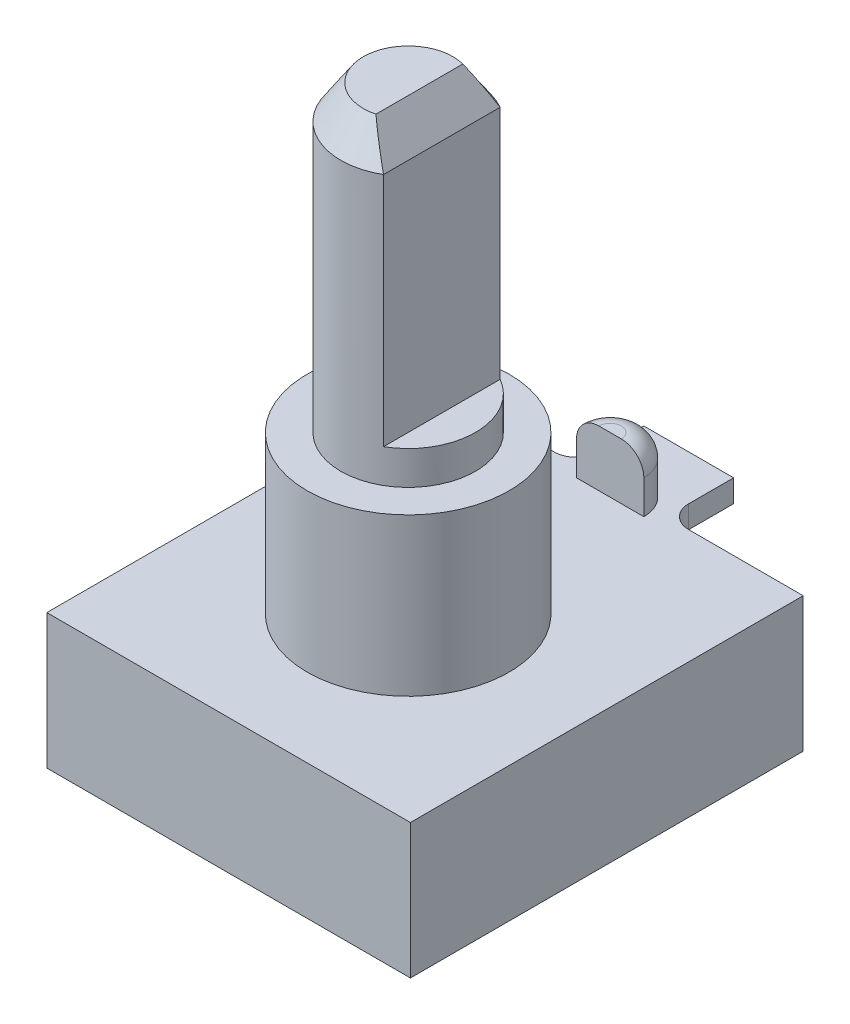
SolidWorks part; units mm, degrees
ref_plane "Front Plane" through (0, 0, 0) normal (0, 0, 1) x (1, 0, 0)
ref_plane "Top Plane" through (0, 0, 0) normal (0, 1, 0) x (1, 0, 0)
ref_plane "Right Plane" through (0, 0, 0) normal (1, 0, 0) x (0, 0, -1)
sketch "Sketch1" plane through (0, 0, 0) normal (0, 1, 0) x (1, 0, 0)
  line L1 (-8.1, 8.75) -> (8.1, 8.75)
  line L2 (-8.1, 8.75) -> (-8.1, -8.75)
  line L3 (-8.1, -8.75) -> (8.1, -8.75)
  line L4 (8.1, 8.75) -> (8.1, -8.75)
  line L5 (-8.1, 8.75) -> (8.1, -8.75) construction
  line L6 (-8.1, -8.75) -> (8.1, 8.75) construction
  point P0 (0, 0)
  dimension "D1" = 17.5
  dimension "D2" = 16.2
extrude "Boss-Extrude1" add sketch "Sketch1" along normal blind 6
sketch "Sketch2" plane through (0, 0, 0) normal (0, -1, 0) x (1, 0, 0)
  line L1 (-6, -6) -> (6, -6)
  line L2 (-6, -6) -> (-6, 6)
  line L3 (-6, 6) -> (6, 6)
  line L4 (6, -6) -> (6, 6)
  line L5 (-6, -6) -> (6, 6) construction
  line L6 (-6, 6) -> (6, -6) construction
  point P0 (0, 0)
  dimension "D1" = 12
  dimension "D2" = 12
extrude "Boss-Extrude2" add sketch "Sketch2" along normal blind 1.5
sketch "Sketch3" plane through (0, 6, 0) normal (0, 1, 0) x (1, 0, 0)
  line L0 (8.1, 8.75) -> (-8.1, 8.75) construction
  circle A0 centre (0, -0.75) radius 4.5
  dimension "D1" = 9
  dimension "D2" = 9.5
extrude "Boss-Extrude3" add sketch "Sketch3" along normal blind 7
sketch "Sketch4" plane through (0, 13, 0) normal (0, 1, 0) x (1, 0, 0)
  circle A0 centre (0, -0.75) radius 3
  dimension "D1" = 6
extrude "Boss-Extrude4" add sketch "Sketch4" along normal blind 13.5
sketch "Sketch5" plane through (0, 26.5, 0) normal (0, 1, 0) x (1, 0, 0)
  line L0 (1.5, 1.8481) -> (1.5, -3.3481)
  circle A0 centre (0, -0.75) radius 3 construction
  arc A1 (1.5, 1.8481) -> (1.5, -3.3481) centre (0, -0.75) ccw
  arc A2 (1.5, 1.8481) -> (1.5, -3.3481) centre (0, -0.75) cw
  point P6 (-3, -0.75)
  circle M3 centre (0, -0.75) radius 3
  dimension "D1" = 4.5
  dimension "D2" = 3
extrude "Cut-Extrude1" cut sketch "Sketch5" against normal blind 12 contours L0 M3
sketch "Sketch6" plane through (0, 0, -8.75) normal (0, 0, -1) x (-1, 0, 0)
  line L0 (-8.1, 6) -> (8.1, 6) construction
  line L1 (-2, 5) -> (2, 5)
  line L2 (-2, 5) -> (-2, 6)
  line L3 (-2, 6) -> (2, 6)
  line L4 (2, 5) -> (2, 6)
  line L5 (-2, 5) -> (2, 6) construction
  line L6 (-2, 6) -> (2, 5) construction
  line L7 (-8.1, 0) -> (8.1, 0) construction
  point P0 (0, 5.5)
  point P9 (0, 0)
  dimension "D1" = 1
  dimension "D2" = 4
  dimension "D3" = 0
extrude "Boss-Extrude5" add sketch "Sketch6" along normal blind 3
fillet "Fillet1" radius 1 2 edges at (-2, 5.5, -8.75) (2, 5.5, -8.75)
chamfer "Chamfer1" distance 1.5 distance2 1 1 edges at (-3, 26.5, 0.75)
chamfer "Chamfer2" distance 1 distance2 1.5 1 edges at (1.5, 26.5, 0.75)
sketch "Sketch7" plane through (0, 6, 0) normal (0, 1, 0) x (1, 0, 0)
  line L0 (-1.5, 8.25) -> (1.5, 8.25)
  line L1 (8.1, 8.75) -> (3, 8.75) construction
  arc A0 (1.5, 8.25) -> (-1.5, 8.25) centre (0, 8.25) ccw
  point P3 (0, 8.25)
  dimension "D1" = 3
  dimension "D2" = 0
  dimension "D3" = 0.5
extrude "Boss-Extrude6" add sketch "Sketch7" along normal blind 2.5
fillet "Fillet2" radius 1 1 edges at (0, 8.5, -9.75)
equation "\"D2@Sketch2\"=\"D1@Sketch2\""
equation "\"D2@Sketch3\"=14-\"D1@Sketch3\"/2"
equation "\"D2@Sketch5\"=\"D1@Sketch4\"/2"
equation "\"D3@Sketch6\"=0"
